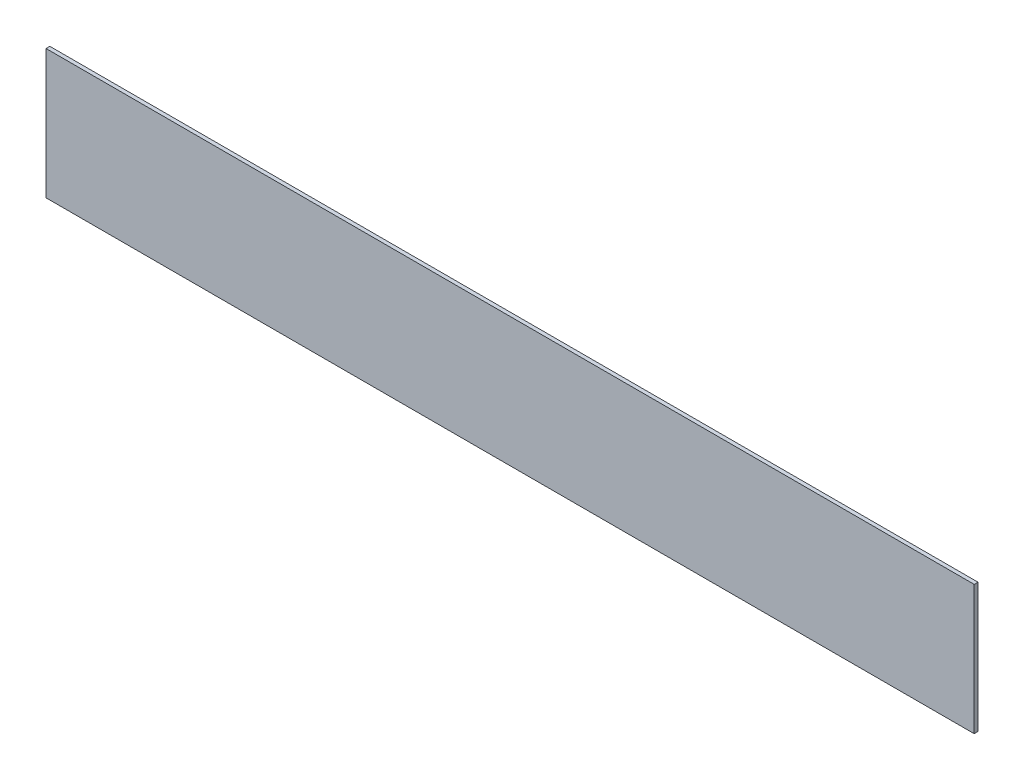
SolidWorks part; units mm, degrees
ref_plane "Front Plane" through (0, 0, 0) normal (0, 0, 1) x (1, 0, 0)
ref_plane "Top Plane" through (0, 0, 0) normal (0, 1, 0) x (1, 0, 0)
ref_plane "Right Plane" through (0, 0, 0) normal (1, 0, 0) x (0, 0, -1)
sketch "Sketch1" plane through (0, 0, 0) normal (0, 0, 1) x (1, 0, 0)
  line L1 (-61, 8.5) -> (61, 8.5)
  line L2 (-61, 8.5) -> (-61, -8.5)
  line L3 (-61, -8.5) -> (61, -8.5)
  line L4 (61, 8.5) -> (61, -8.5)
  line L5 (0, -8.5) -> (0, 8.5) construction
  line L6 (-61, 0) -> (61, 0) construction
  point P0 (0, 0)
  dimension "D1" = 122
  dimension "D2" = 17
extrude "Boss-Extrude1" add sketch "Sketch1" along normal blind 0.5
